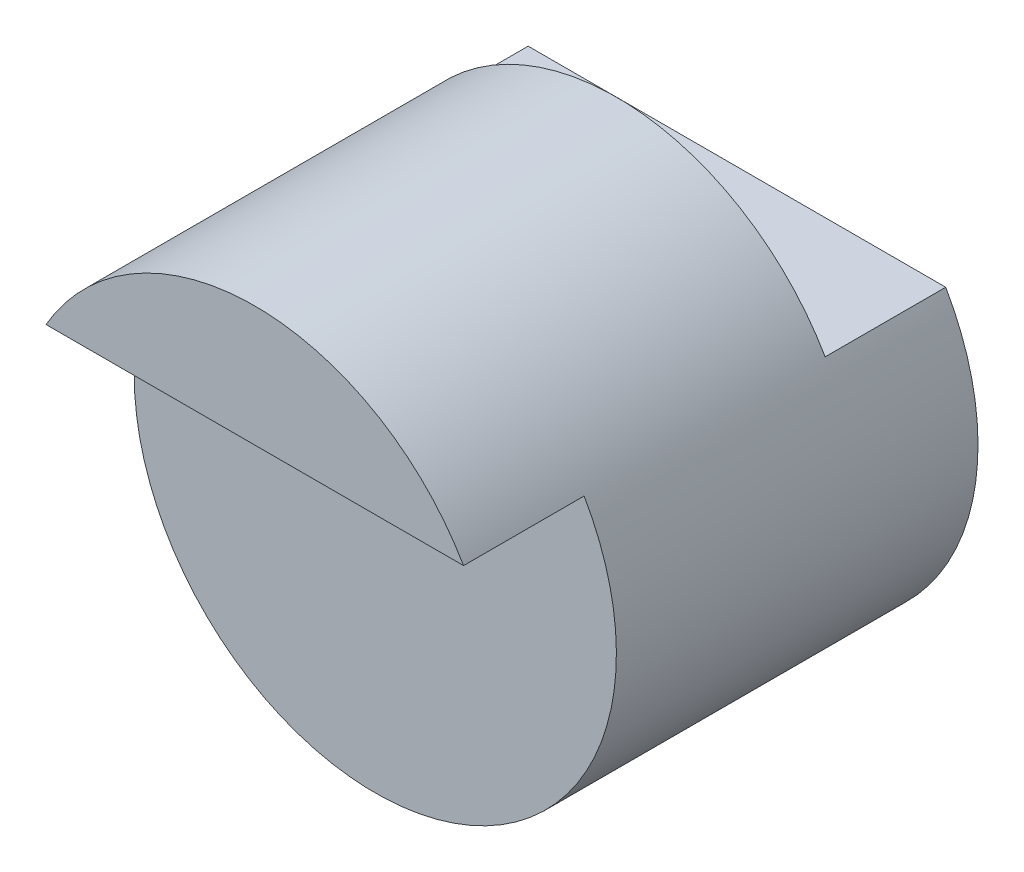
SolidWorks part; units mm, degrees
ref_plane "Front" through (0, 0, 0) normal (0, 0, 1) x (1, 0, 0)
ref_plane "Top" through (0, 0, 0) normal (0, 1, 0) x (1, 0, 0)
ref_plane "Right" through (0, 0, 0) normal (1, 0, 0) x (0, 0, -1)
sketch "Sketch1" plane through (0, 0, 0) normal (0, 0, 1) x (1, 0, 0)
  circle A0 centre (0, 0) radius 2
  dimension "D1" = 4
extrude "Boss-Extrude1" add sketch "Sketch1" along normal blind 3
sketch "Sketch2" plane through (0, 0, 3) normal (0, 0, 1) x (1, 0, 0)
  line L0 (-1.7321, 1) -> (1.7321, 1)
  circle A0 centre (0, 0) radius 2 construction
  arc A1 (-1.7321, 1) -> (1.7321, 1) centre (0, 0) cw
  dimension "D1" = 1
extrude "Boss-Extrude2" add sketch "Sketch2" along normal blind 1
sketch "Sketch3" plane through (0, 0, 0) normal (0, 0, -1) x (-1, 0, 0)
  line L0 (1.7321, 1) -> (-1.7321, 1)
  arc A0 (1.7321, 1) -> (-1.7321, 1) centre (0, 0) ccw
extrude "Cut-Extrude1" cut sketch "Sketch3" against normal blind 1
